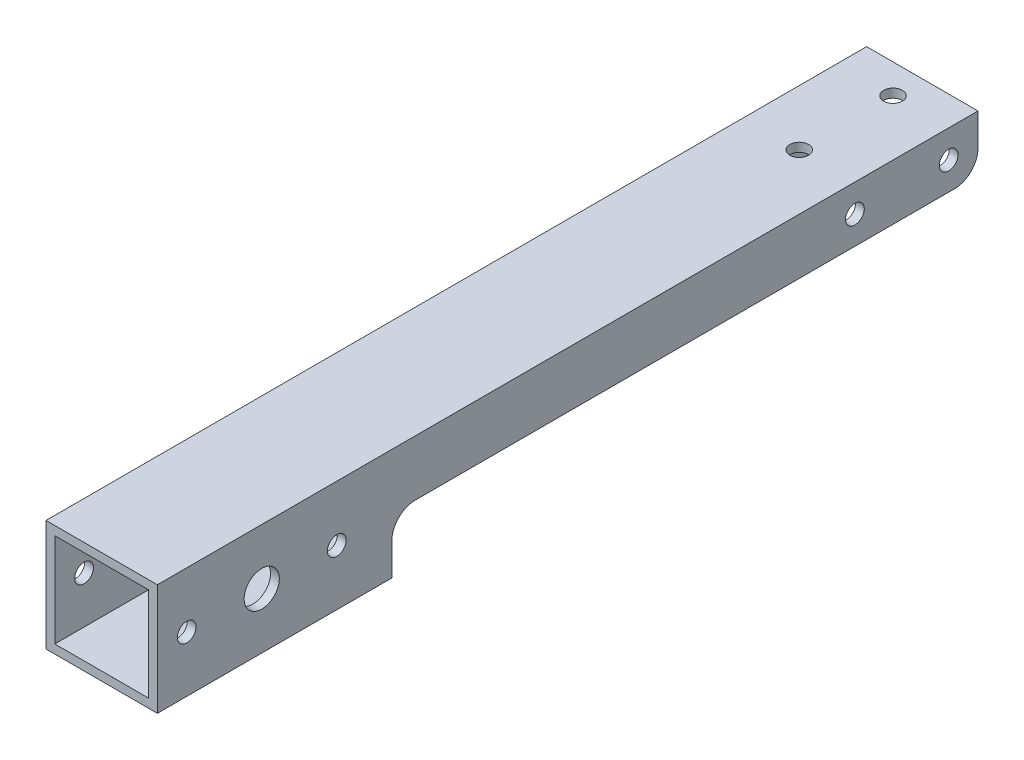
SolidWorks part; units mm, degrees
material "Gerais  - 6061-T6"
ref_plane "Plano frontal" through (0, 0, 0) normal (0, 0, 1) x (1, 0, 0)
ref_plane "Plano superior" through (0, 0, 0) normal (0, 1, 0) x (1, 0, 0)
ref_plane "Plano direito" through (0, 0, 0) normal (1, 0, 0) x (0, 0, -1)
sketch "Esboço1" plane through (0, 0, 0) normal (0, 0, 1) x (1, 0, 0)
  line L1 (-9.5, -9.5) -> (9.5, -9.5)
  line L2 (-9.5, -9.5) -> (-9.5, 9.5)
  line L3 (-9.5, 9.5) -> (9.5, 9.5)
  line L4 (9.5, -9.5) -> (9.5, 9.5)
  line L5 (0, 9.5) -> (0, -9.5) construction
  line L6 (-9.5, 0) -> (9.5, 0) construction
  line L7 (8, -8) -> (-8, -8)
  line L8 (8, -8) -> (8, 8)
  line L9 (8, 8) -> (-8, 8)
  line L10 (-8, -8) -> (-8, 8)
  line L11 (0, 8) -> (0, -8) construction
  line L12 (8, 0) -> (-8, 0) construction
  point P0 (0, 0)
  point P4 (0, 0)
  dimension "D1" = 19
  dimension "D2" = 1.5
extrude "Ressalto-extrusão1" add sketch "Esboço1" along normal blind 140 contours L3 L4 L1 L2 | L8 L7 L10 L9
sketch "Esboço2" plane through (9.5, 0, 0) normal (1, 0, 0) x (0, 0, -1)
  line L0 (-161.3966, 22.4643) -> (-181.3966, 6.4643) construction
  line L1 (0, -9.5) -> (0, 9.5) construction
  line L2 (-161.3966, 6.4643) -> (-181.3966, 6.4643) construction
  line L3 (-161.3966, 6.4643) -> (-161.3966, 22.4643) construction
  line L4 (-161.3966, 22.4643) -> (-181.3966, 22.4643) construction
  line L5 (-181.3966, 6.4643) -> (-181.3966, 22.4643) construction
  line L6 (-171.3966, 22.4643) -> (-171.3966, 6.4643) construction
  line L7 (-161.3966, 14.4643) -> (-181.3966, 14.4643) construction
  line L8 (-135, 0) -> (-109.3875, 0) construction
  line L9 (-140, -9.5) -> (-140, 9.5) construction
  line L10 (-12.0679, 0) -> (-12.0679, 9.5) construction
  line L11 (-140, 9.5) -> (0, 9.5) construction
  circle A5 centre (-135, 0) radius 1.6
  circle A6 centre (-122.1938, 0) radius 3
  circle A7 centre (-109.3875, 0) radius 1.6
  circle A8 centre (-5, 4.75) radius 1.6
  circle A9 centre (-21, 4.75) radius 1.6
  point P6 (-171.3966, 14.4643)
  point P13 (-140, 0)
  point P24 (-12.0679, 4.75)
  dimension "D1" = 6
  dimension "D5" = 3.2
  dimension "D8" = 3.2
  dimension "D2" = 16
  dimension "D3" = 20
  dimension "D4" = 5
  dimension "D6" = 16
  dimension "D7" = 5
extrude "Corte-extrusão1" cut sketch "Esboço2" against normal through all contours A7 | A5 | A6 | A8 | A9
sketch "Esboço3" plane through (0, 9.5, 0) normal (0, 1, 0) x (1, 0, 0)
  line L0 (0, -21) -> (0, -5) construction
  line L1 (-9.5, 0) -> (9.5, 0) construction
  circle A1 centre (0, -21) radius 1.6
  circle A2 centre (0, -5) radius 1.6
  dimension "D2" = 3.2
  dimension "D1" = 16
  dimension "D4" = 5
extrude "Corte-extrusão2" cut sketch "Esboço3" against normal up to surface (1.5 mm away) up to face at (0, 8, 70)
sketch "Esboço5" plane through (0, 0, 0) normal (0, 0, -1) x (-1, 0, 0)
  line L0 (-9.5, -9.5) -> (-9.5, 9.5) construction
  line L1 (9.5, -9.5) -> (-9.5, -9.5)
  line L2 (9.5, -9.5) -> (9.5, 0)
  line L3 (9.5, 0) -> (-9.5, 0)
  line L4 (-9.5, -9.5) -> (-9.5, 0)
extrude "Corte-extrusão4" cut sketch "Esboço5" against normal offset from surface (100 mm away) 40 up to face at (0, 0, 140)
fillet "Filete1" radius 4 4 edges at (-8.75, 0, 100) (8.75, 0, 100) (-8.75, 0, 0) (8.75, 0, 0)
